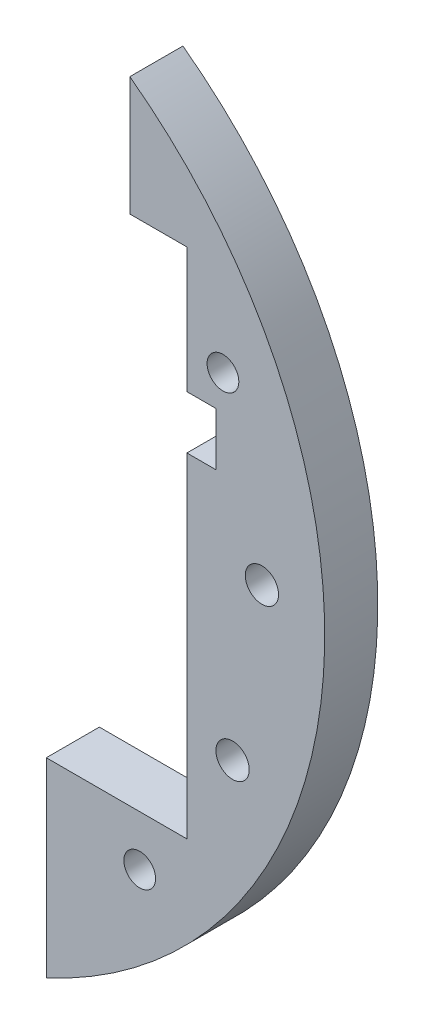
SolidWorks part; units mm, degrees
material "Balsa"
ref_plane "Front Plane" through (0, 0, 0) normal (0, 0, 1) x (1, 0, 0)
ref_plane "Top Plane" through (0, 0, 0) normal (0, 1, 0) x (1, 0, 0)
ref_plane "Right Plane" through (0, 0, 0) normal (1, 0, 0) x (0, 0, -1)
sketch "Sketch1" plane through (0, 0, 0) normal (0, 0, 1) x (1, 0, 0)
  line L0 (45.3154, 21.1309) -> (0, 0) construction
  line L1 (0, 0) -> (35.3553, -35.3553) construction
  line L2 (49.9788, 1.4542) -> (0, 0) construction
  line L3 (0, 0) -> (46.4674, -18.4603) construction
  circle A0 centre (45.3154, 21.1309) radius 1.8986
  circle A1 centre (46.4674, -18.4603) radius 1.9939
  circle A2 centre (0, 0) radius 57.5
  circle A3 centre (0, 0) radius 8
  circle A4 centre (49.9788, 1.4542) radius 1.9939
  circle A5 centre (0, 0) radius 40 construction
  circle A6 centre (0, 0) radius 50 construction
  circle A29 centre (0, -40) radius 1.9939
  circle A30 centre (0, -50) radius 1.8986
  circle A37 centre (-28.2843, -28.2843) radius 1.9939
  circle A38 centre (-35.3553, -35.3553) radius 1.8986
  circle A39 centre (-40, 0) radius 1.9939
  circle A40 centre (-50, 0) radius 1.8986
  circle A41 centre (-28.2843, 28.2843) radius 1.9939
  circle A42 centre (-35.3553, 35.3553) radius 1.8986
  circle A43 centre (0, 40) radius 1.9939
  circle A44 centre (0, 50) radius 1.8986
  circle A45 centre (28.2843, 28.2843) radius 1.9939 construction
  circle A46 centre (35.3553, 35.3553) radius 1.8986 construction
  circle A47 centre (40, 0) radius 1.9939 construction
  circle A48 centre (50, 0) radius 1.8986 construction
  circle A49 centre (28.2843, -28.2843) radius 1.9939 construction
  circle A50 centre (35.3553, -35.3553) radius 1.8986
  dimension "D1" = 115
  dimension "D4" = 3.7973
  dimension "D6" = 100
  dimension "D7" = 80
  dimension "D8" = 3.9878
  dimension "D9" = 3.9878
  dimension "D10" = 23.333
  dimension "D15" = 3.7973
  dimension "D16" = 3.9878
  dimension "D5" = 70
  dimension "D3" = 16
  dimension "D11" = 23.333
  dimension "D21" = 8
extrude "Boss-Extrude1" add sketch "Sketch1" along normal blind 6.35
sketch "Sketch2" plane through (0, 0, 0) normal (0, 0, 1) x (1, 0, 0)
  line L0 (12.5, -29.35) -> (41, -29.35)
  line L1 (41, -29.35) -> (41, 10.65)
  line L2 (41, 10.65) -> (44.5, 10.65)
  line L3 (44.5, 10.65) -> (44.5, 17)
  line L4 (44.5, 17) -> (41, 17)
  line L5 (41, 17) -> (41, 32)
  line L6 (41, 32) -> (21, 32)
  line L7 (21, 32) -> (21, 17)
  line L8 (21, 17) -> (17.5, 17)
  line L9 (17.5, 17) -> (17.5, 10.65)
  line L10 (17.5, 10.65) -> (21, 10.65)
  line L11 (21, 10.65) -> (21, 5.65)
  line L12 (21, 5.65) -> (12.5, 5.65)
  line L13 (12.5, 5.65) -> (12.5, -29.35)
  dimension "D2" = 20
  dimension "D3" = 3.5
  dimension "D4" = 3.5
  dimension "D5" = 15
  dimension "D6" = 21
  dimension "D7" = 6.35
  dimension "D8" = 5
  dimension "D9" = 40
  dimension "D10" = 8.5
  dimension "D11" = 32
extrude "Cut-Extrude1" cut sketch "Sketch2" along normal through all
sketch "Sketch3" plane through (0, 0, 6.35) normal (0, 0, 1) x (1, 0, 0)
  line L0 (41, 32) -> (21, 32) construction
  line L1 (27.825, -8) -> (34.175, -8)
  line L2 (27.825, -8) -> (27.825, 72)
  line L3 (27.825, 72) -> (34.175, 72)
  line L4 (34.175, -8) -> (34.175, 72)
  line L5 (27.825, -8) -> (34.175, 72) construction
  line L6 (27.825, 72) -> (34.175, -8) construction
  point P0 (31, 32)
  dimension "D1" = 6.35
  dimension "D2" = 80
extrude "Cut-Extrude3" cut sketch "Sketch3" against normal through all
sketch "Sketch4" plane through (0, 0, 6.35) normal (0, 0, 1) x (1, 0, 0)
  line L0 (21, -36.5) -> (21, -16.443)
  line L1 (27.825, 32) -> (34.175, 32) construction
  line L2 (21, -16.443) -> (24.175, -16.4703)
  line L3 (24.175, -16.4703) -> (24.175, -57.5)
  line L4 (0, -57.5) -> (24.175, -57.5)
  line L5 (0, 0) -> (98.5911, 0) construction
  line L6 (0, 57.5) -> (24.175, 57.5)
  line L7 (24.175, 16.4703) -> (24.175, 57.5)
  line L8 (21, 16.443) -> (24.175, 16.4703)
  line L9 (21, 36.5) -> (21, 16.443)
  arc A0 (0, -57.5) -> (21, -36.5) centre (0, -36.5) ccw
  arc A1 (0, 57.5) -> (21, 36.5) centre (0, 36.5) cw
  arc A2 (27.825, 50.3192) -> (34.175, 46.242) centre (0, 0) ccw construction
  point P13 (31, 32)
  point P14 (22.5875, -16.4566)
  dimension "D3" = 3.175
  dimension "D4" = 8.4125
extrude "Cut-Extrude4" cut sketch "Sketch4" against normal through all
sketch "Sketch5" plane through (0, 0, 6.35) normal (0, 0, 1) x (1, 0, 0)
  line L3 (24.175, 52.1711) -> (24.175, 32)
  line L4 (24.175, 52.1711) -> (24.175, 32)
  line L5 (24.175, 32) -> (27.825, 32)
  line L6 (24.175, 32) -> (27.825, 32)
  line L7 (27.825, 32) -> (27.825, 50.3192)
  line L8 (27.825, 32) -> (27.825, 50.3192)
  arc A1 (27.825, 50.3192) -> (24.175, 52.1711) centre (0, 0) ccw
  arc A2 (27.825, 50.3192) -> (24.175, 52.1711) centre (0, 0) ccw
  dimension "D1" = 0
extrude "Cut-Extrude5" cut sketch "Sketch5" against normal through all
